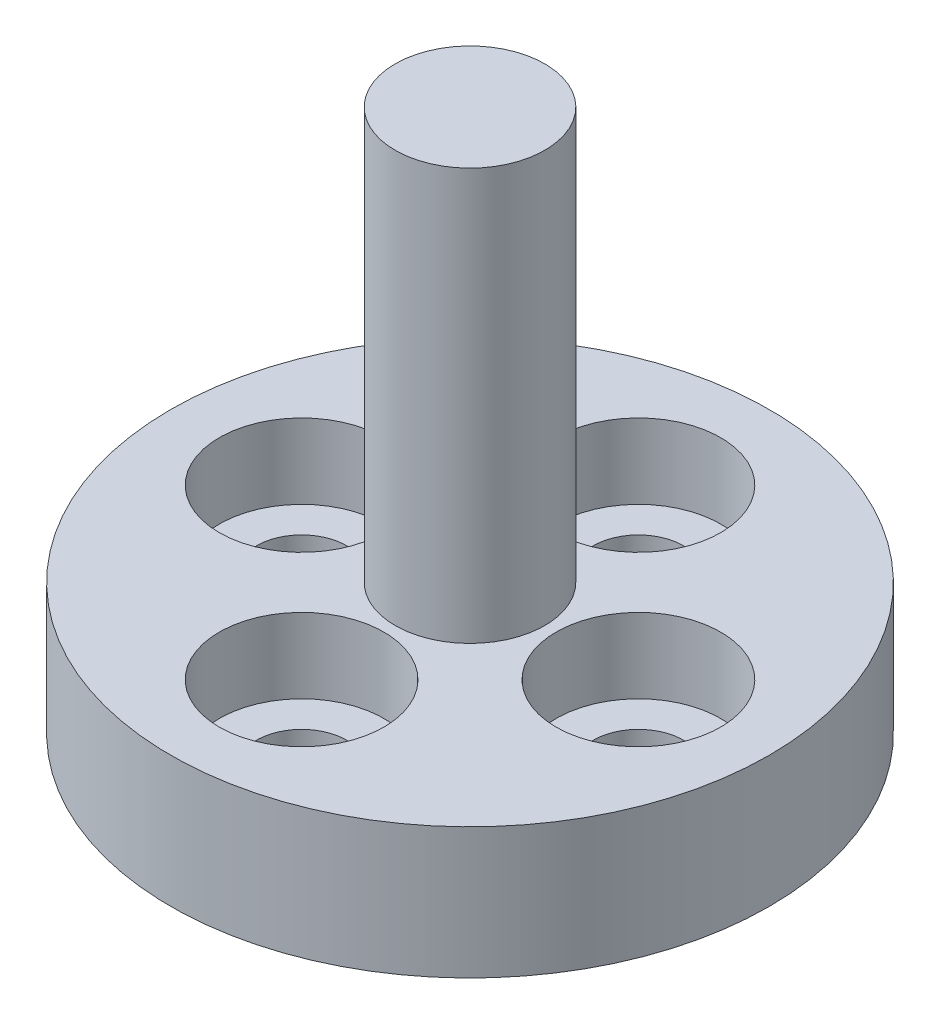
SolidWorks part; units mm, degrees
ref_plane "Front Plane" through (0, 0, 0) normal (0, 0, 1) x (1, 0, 0)
ref_plane "Top Plane" through (0, 0, 0) normal (0, 1, 0) x (1, 0, 0)
ref_plane "Right Plane" through (0, 0, 0) normal (1, 0, 0) x (0, 0, -1)
sketch "Sketch1" plane through (0, 0, 0) normal (0, 0, 1) x (1, 0, 0)
  line L0 (0, 0) -> (8, 0)
  line L1 (8, 0) -> (8, 3.5)
  line L2 (8, 3.5) -> (2, 3.5)
  line L3 (2, 3.5) -> (2, 14.5)
  line L4 (2, 14.5) -> (0, 14.5)
  line L5 (0, 14.5) -> (0, 0)
  dimension "D1" = 8
  dimension "D2" = 14.5
  dimension "D3" = 11
  dimension "D4" = 2
revolve "Revolve1" add sketch "Sketch1" angle 360 about L5
sketch "Sketch2" plane through (0, 3.5, 0) normal (0, 1, 0) x (1, 0, 0)
  circle A0 centre (0, 0) radius 4.5
  dimension "D1" = 9
hole_wizard "CBORE for M2 SHCS1" positions "Sketch7" profile "Sketch8" counterbore size "M2" standard "ANSI Metric" end condition through all
sketch "Sketch7" plane through (0, 3.5, 0) normal (0, 1, 0) x (1, 0, 0)
  circle A0 centre (0, 0) radius 4.5 construction
  point P0 (-4.5, 0)
  point P4 (0, 4.5)
  point P6 (4.5, 0)
  point P8 (0, -4.5)
sketch "Sketch8" plane through (-4.5, 3.5, 0) normal (1, 0, 0) x (0, 0, 1)
  line L0 (0, 0) -> (0, 3.5)
  line L1 (0, 3.5) -> (1.2, 3.5)
  line L3 (1.2, 3.5) -> (1.2, 2)
  line L4 (1.2, 2) -> (2.2, 2)
  line L5 (2.2, 2) -> (2.2, 0)
  line L7 (2.2, 0) -> (0, 0)
  line L11 (0, -6.35) -> (0, 107.95) construction
  dimension "Thru Hole Dia." = 2.4
  dimension "Thru Hole Depth" = 3.5
  dimension "C'Bore Dia." = 4.4
  dimension "C'Bore Depth" = 2
